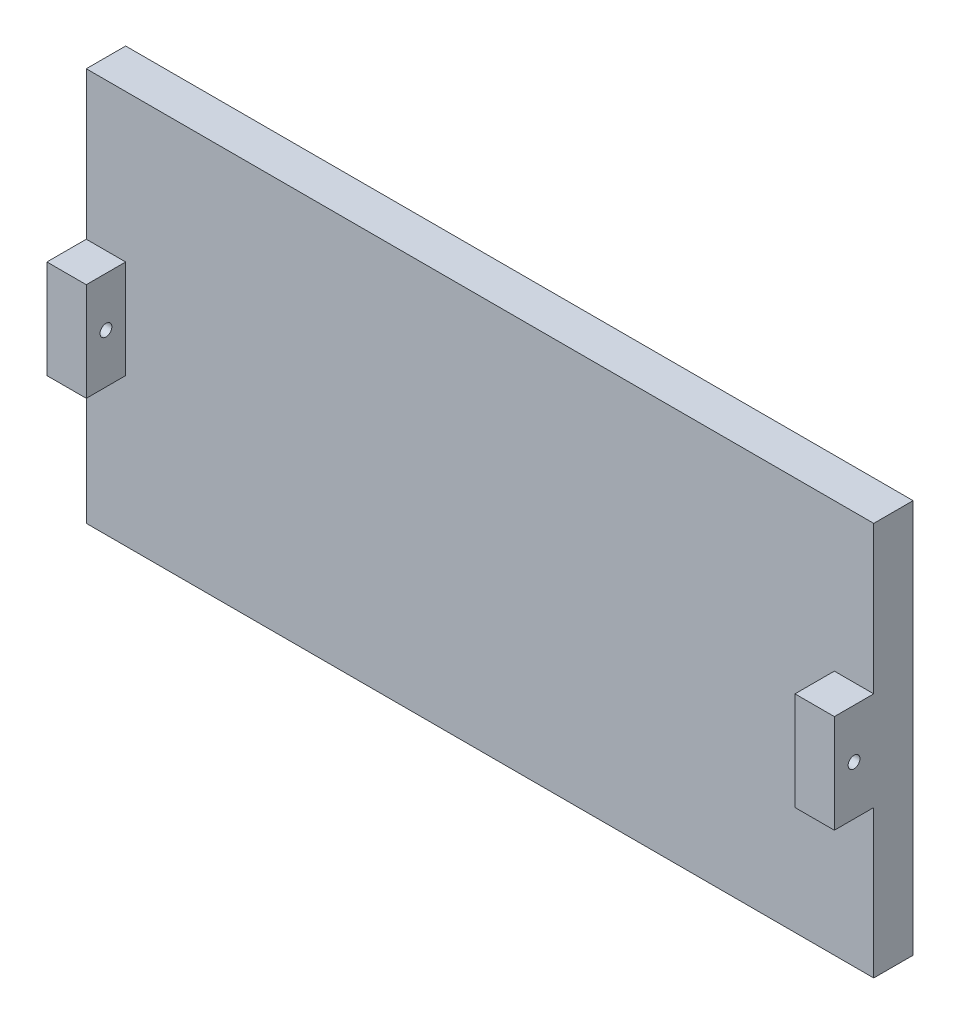
SolidWorks part; units mm, degrees
ref_plane "Plan de face" through (0, 0, 0) normal (0, 0, 1) x (1, 0, 0)
ref_plane "Plan de dessus" through (0, 0, 0) normal (0, 1, 0) x (1, 0, 0)
ref_plane "Plan de droite" through (0, 0, 0) normal (1, 0, 0) x (0, 0, -1)
sketch "Esquisse1" plane through (0, 0, 0) normal (0, 0, 1) x (1, 0, 0)
  line L0 (-100, 0) -> (-100, 110.1242) construction
  line L1 (-200, 100) -> (0, 100)
  line L2 (-200, 100) -> (-200, 0)
  line L3 (-200, 0) -> (0, 0)
  line L4 (0, 100) -> (0, 0)
  dimension "D1" = 100
  dimension "D2" = 200
  dimension "D3" = 100
extrude "Boss.-Extru.1" add sketch "Esquisse1" along normal blind 10
sketch "Esquisse2" plane through (0, 0, 10) normal (0, 0, 1) x (1, 0, 0)
  line L0 (-200, 100) -> (-200, 0) construction
  line L1 (-200, 62.5) -> (-190, 62.5)
  line L2 (-200, 62.5) -> (-200, 37.5)
  line L3 (-200, 37.5) -> (-190, 37.5)
  line L4 (-190, 62.5) -> (-190, 37.5)
  line L5 (-100, 0) -> (-100, 111.1731) construction
  line L6 (-200, 0) -> (0, 0) construction
  line L7 (0, 62.5) -> (-10, 62.5)
  line L8 (-10, 62.5) -> (-10, 37.5)
  line L9 (0, 37.5) -> (-10, 37.5)
  line L10 (0, 62.5) -> (0, 37.5)
  dimension "D1" = 100
  dimension "D2" = 10
  dimension "D3" = 25
  dimension "D4" = 37.5
extrude "Boss.-Extru.2" add sketch "Esquisse2" along normal blind 10
sketch "Esquisse3" plane through (-200, 0, 0) normal (-1, 0, 0) x (0, 0, 1)
  line L1 (20, 62.5) -> (10, 62.5) construction
  line L3 (20, 62.5) -> (20, 37.5) construction
  circle A0 centre (15, 50) radius 1.5
  dimension "D1" = 3
  dimension "D2" = 12.5
  dimension "D3" = 5
extrude "Enlèv. mat.-Extru.1" cut sketch "Esquisse3" against normal through all
